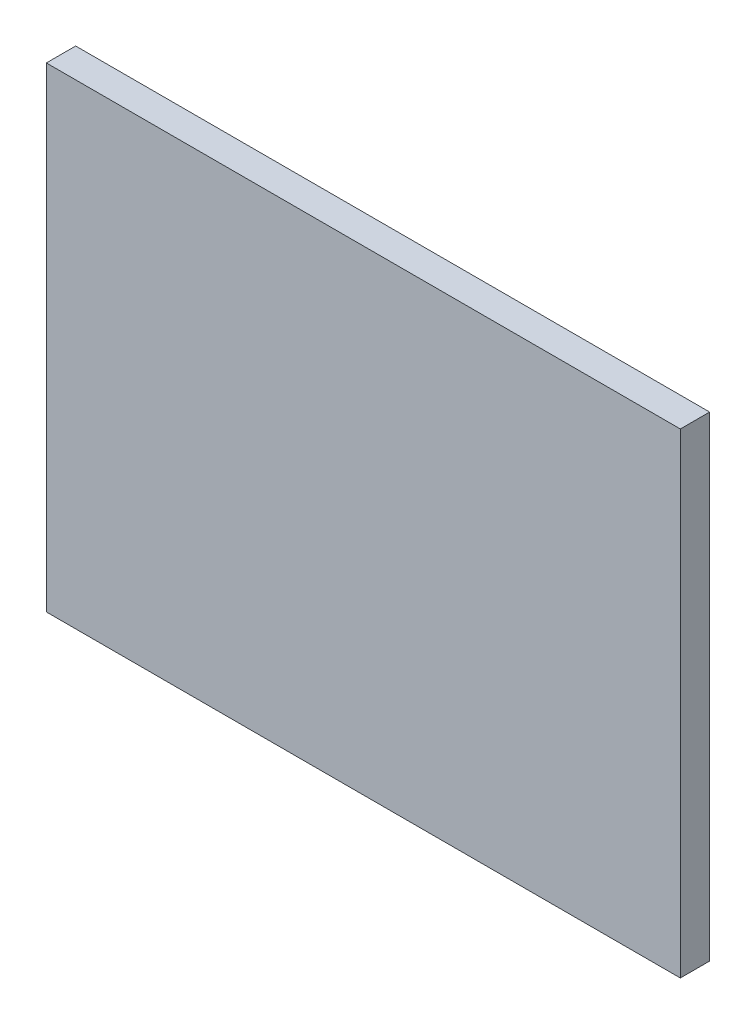
SolidWorks part; units mm, degrees
ref_plane "Front Plane" through (0, 0, 0) normal (0, 0, 1) x (1, 0, 0)
ref_plane "Top Plane" through (0, 0, 0) normal (0, 1, 0) x (1, 0, 0)
ref_plane "Right Plane" through (0, 0, 0) normal (1, 0, 0) x (0, 0, -1)
sketch "Sketch1" plane through (0, 0, 0) normal (0, 0, 1) x (1, 0, 0)
  line L1 (0, 0) -> (203.2, 0)
  line L2 (0, 0) -> (0, 152.4)
  line L3 (0, 152.4) -> (203.2, 152.4)
  line L4 (203.2, 0) -> (203.2, 152.4)
  dimension "D1" = 152.4
  dimension "D2" = 203.2
extrude "Boss-Extrude1" add sketch "Sketch1" along normal blind 9.398
